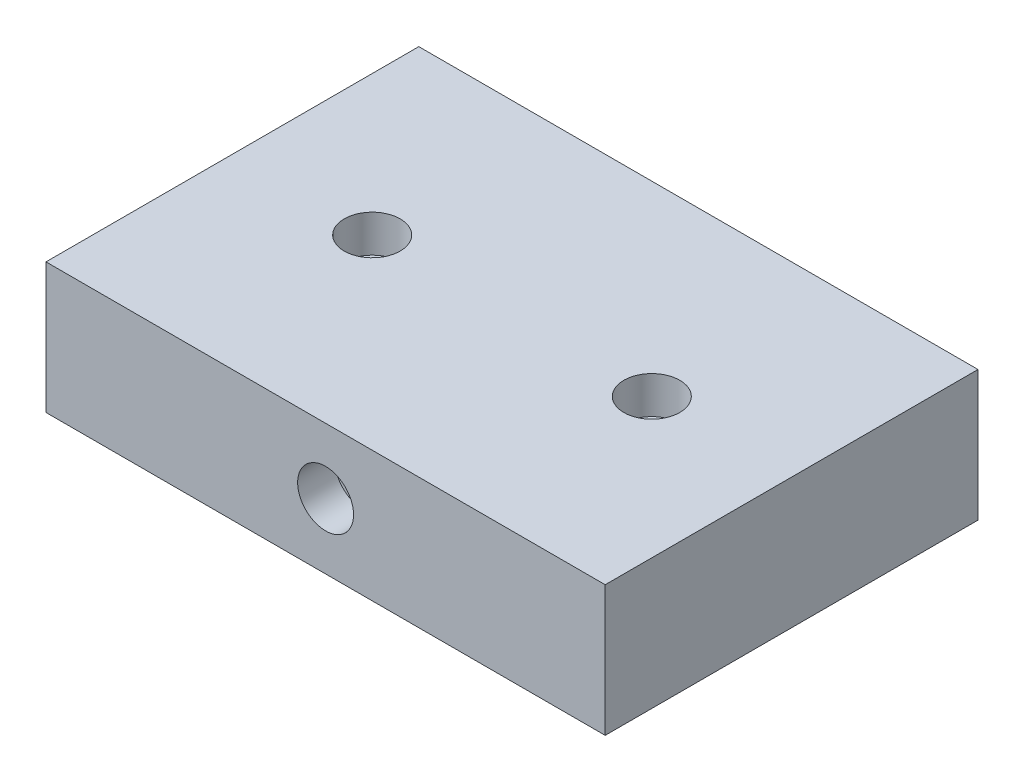
SolidWorks part; units mm, degrees
ref_plane "Front Plane" through (0, 0, 0) normal (0, 0, 1) x (1, 0, 0)
ref_plane "Top Plane" through (0, 0, 0) normal (0, 1, 0) x (1, 0, 0)
ref_plane "Right Plane" through (0, 0, 0) normal (1, 0, 0) x (0, 0, -1)
sketch "Sketch1" plane through (0, 0, 0) normal (0, 0, 1) x (1, 0, 0)
  line L1 (0, 0) -> (30, 0)
  line L2 (0, 0) -> (0, 7)
  line L3 (0, 7) -> (30, 7)
  line L4 (30, 0) -> (30, 7)
  dimension "D1" = 30
  dimension "D2" = 7
extrude "Boss-Extrude1" add sketch "Sketch1" along normal blind 20
sketch "Sketch2" plane through (0, 0, 20) normal (0, 0, 1) x (1, 0, 0)
  line L0 (15, 7) -> (15, 0) construction
  line L1 (30, 7) -> (0, 7) construction
  line L2 (0, 0) -> (30, 0) construction
  circle A0 centre (15, 3.5) radius 1.5
  dimension "D1" = 3
extrude "Cut-Extrude1" cut sketch "Sketch2" against normal blind 2
sketch "Sketch3" plane through (0, 7, 0) normal (0, 1, 0) x (1, 0, 0)
  line L1 (0, -20) -> (0, 0) construction
  line L2 (30, -20) -> (30, 0) construction
  line L3 (30, -10) -> (15, -10) construction
  line L4 (15, -10) -> (0, -10) construction
  line L5 (0, -10) -> (15, -10) construction
  line L6 (15, -10) -> (30, -10) construction
  circle A0 centre (7.5, -10) radius 1.5
  circle A1 centre (22.5, -10) radius 1.5
  dimension "D1" = 3
extrude "Cut-Extrude2" cut sketch "Sketch3" against normal blind 2
